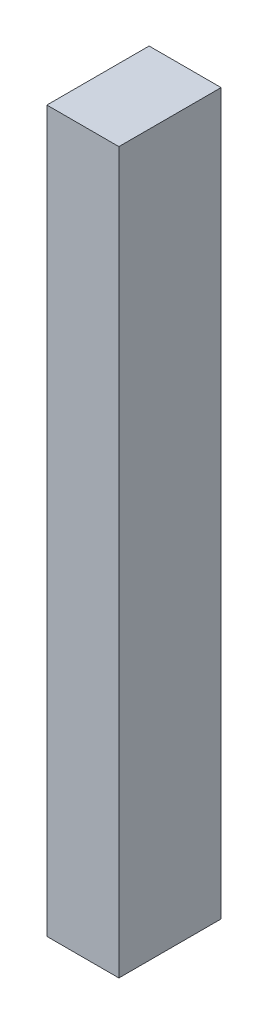
SolidWorks part; units mm, degrees
ref_plane "Front Plane" through (0, 0, 0) normal (0, 0, 1) x (1, 0, 0)
ref_plane "Top Plane" through (0, 0, 0) normal (0, 1, 0) x (1, 0, 0)
ref_plane "Right Plane" through (0, 0, 0) normal (1, 0, 0) x (0, 0, -1)
sketch "Sketch1" plane through (0, 0, 0) normal (0, 0, 1) x (1, 0, 0)
  line L1 (0, 0) -> (20, 0)
  line L2 (0, 0) -> (0, 200)
  line L3 (0, 200) -> (20, 200)
  line L4 (20, 0) -> (20, 200)
  dimension "D1" = 20
  dimension "D2" = 200
extrude "Boss-Extrude1" add sketch "Sketch1" along normal blind 28.4
